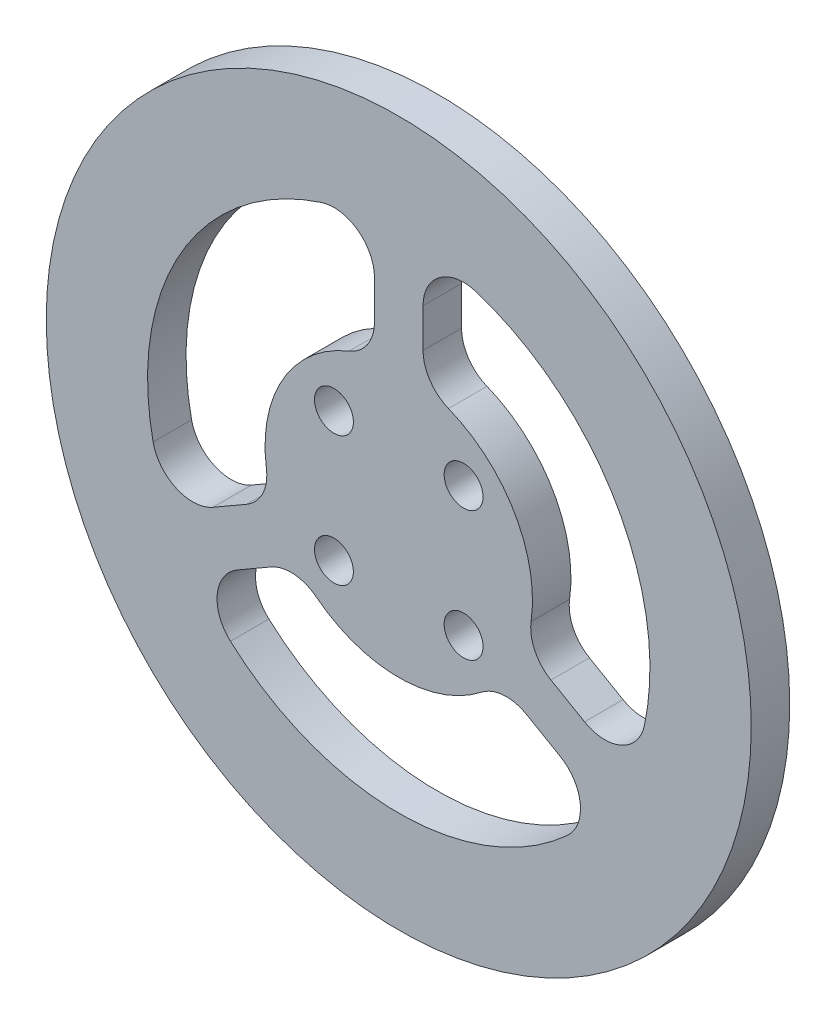
SolidWorks part; units mm, degrees
material "Cast Carbon Steel"
ref_plane "Front Plane" through (0, 0, 0) normal (0, 0, 1) x (1, 0, 0)
ref_plane "Top Plane" through (0, 0, 0) normal (0, 1, 0) x (1, 0, 0)
ref_plane "Right Plane" through (0, 0, 0) normal (1, 0, 0) x (0, 0, -1)
sketch "Sketch1" plane through (0, 0, 0) normal (0, 0, 1) x (1, 0, 0)
  circle A0 centre (0, 0) radius 43.5
  dimension "D1" = 87
extrude "Boss-Extrude1" add sketch "Sketch1" along normal blind 4.7498
sketch "Sketch2" plane through (0, 0, 4.7498) normal (0, 0, 1) x (1, 0, 0)
  circle A0 centre (0, 0) radius 31
  circle A1 centre (0, 0) radius 16.5
  dimension "D1" = 62
  dimension "D2" = 33
extrude "Cut-Extrude1" cut sketch "Sketch2" against normal blind 21.73
sketch "Sketch3" plane through (0, 0, 4.7498) normal (0, 0, 1) x (1, 0, 0)
  line L0 (-3, 16.225) -> (-3, 30.8545)
  line L1 (3, 16.225) -> (3, 30.8545)
  line L2 (0, -2.6124) -> (0, 2.6124) construction
  line L3 (-3, 23.5397) -> (0, 23.5397) construction
  line L4 (3, 23.5397) -> (0, 23.5397) construction
  circle A0 centre (0, 0) radius 16.5 construction
  circle A1 centre (0, 0) radius 31 construction
  arc A2 (3, 16.225) -> (-3, 16.225) centre (0, 0) ccw
  arc A3 (3, 30.8545) -> (-3, 30.8545) centre (0, 0) ccw
  dimension "D1" = 6
extrude "Boss-Extrude2" add sketch "Sketch3" against normal up to surface (4.7498 mm away) up to face at (16.5, 0, 0)
pattern_circular "CirPattern1" count 3 over 360 about axis through (0, 0, 0) along (0, 0, 1) of "Boss-Extrude2"
fillet "Fillet1" radius 5 12 edges at (28.2208, -12.8292, 2.3749) (3, 30.8545, 2.3749) (3, 16.225, 2.3749) (15.5512, -5.5144, 2.3749) (25.2208, -18.0253, 2.3749) (12.5512, -10.7106, 2.3749) (-12.5512, -10.7106, 2.3749) (-25.2208, -18.0253, 2.3749) (-28.2208, -12.8292, 2.3749) (-15.5512, -5.5144, 2.3749) (-3, 16.225, 2.3749) (-3, 30.8545, 2.3749)
sketch "Sketch4" plane through (0, 0, 4.7498) normal (0, 0, 1) x (1, 0, 0)
  line L1 (-8, 8) -> (8, 8) construction
  line L2 (-8, 8) -> (-8, -8) construction
  line L3 (-8, -8) -> (8, -8) construction
  line L4 (8, 8) -> (8, -8) construction
  line L5 (-8, 8) -> (8, -8) construction
  line L6 (-8, -8) -> (8, 8) construction
  point P0 (0, 0)
  point P7 (-8, 8)
  point P8 (-8, -8)
  point P9 (8, -8)
  point P10 (8, 8)
  dimension "D1" = 16
sketch "Sketch5" plane through (0, 0, 4.7498) normal (0, 0, 1) x (1, 0, 0)
  point P0 (-8, 8)
  point P3 (-8, -8)
  point P6 (8, -8)
  point P9 (8, 8)
hole_wizard "M4 Clearance Hole1" positions "Sketch5" profile "Sketch6" hole size "M4" standard "ANSI Metric" end condition through all
sketch "Sketch6" plane through (-8, 8, 4.7498) normal (1, 0, 0) x (0, -1, 0)
  line L0 (0, 0) -> (0, 4.7498)
  line L1 (0, 4.7498) -> (2.4, 4.7498)
  line L2 (2.4, 4.7498) -> (2.4, 0)
  line L5 (2.4, 0) -> (0, 0)
  line L11 (0, -6.35) -> (0, 107.95) construction
  dimension "Thru Hole Dia." = 4.8
  dimension "Thru Hole Depth" = 4.7498
